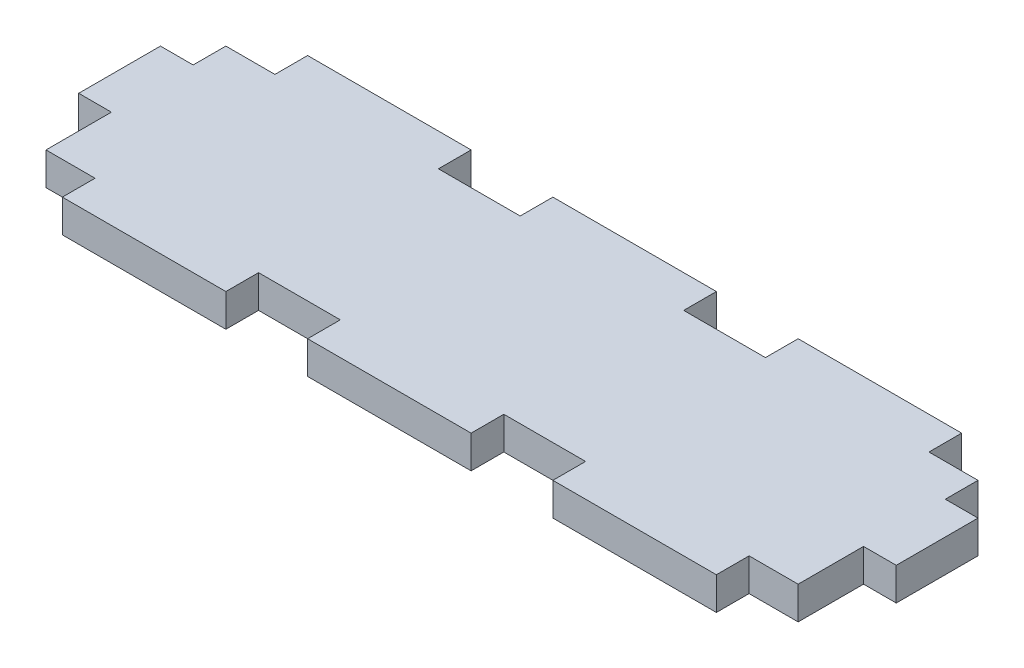
SolidWorks part; units mm, degrees
ref_plane "Front Plane" through (0, 0, 0) normal (0, 0, 1) x (1, 0, 0)
ref_plane "Top Plane" through (0, 0, 0) normal (0, 1, 0) x (1, 0, 0)
ref_plane "Right Plane" through (0, 0, 0) normal (1, 0, 0) x (0, 0, -1)
sketch "Sketch1" plane through (0, 0, 0) normal (0, 1, 0) x (1, 0, 0)
  line L1 (63.5, -19.05) -> (-63.5, -19.05)
  line L2 (63.5, -19.05) -> (63.5, 19.05)
  line L3 (63.5, 19.05) -> (-63.5, 19.05)
  line L4 (-63.5, -19.05) -> (-63.5, 19.05)
  line L5 (63.5, -19.05) -> (-63.5, 19.05) construction
  line L6 (63.5, 19.05) -> (-63.5, -19.05) construction
  point P0 (0, 0)
  dimension "D1" = 127
  dimension "D2" = 38.1
extrude "Boss-Extrude1" add sketch "Sketch1" along normal mid plane 5.08
sketch "Sketch2" plane through (0, 2.54, 0) normal (0, 1, 0) x (1, 0, 0)
  line L0 (63.5, 19.05) -> (-63.5, 19.05) construction
  line L1 (-63.5, 19.05) -> (-58.42, 19.05)
  line L2 (-63.5, 19.05) -> (-63.5, 8.89)
  line L3 (-63.5, 8.89) -> (-58.42, 8.89)
  line L4 (-58.42, 19.05) -> (-58.42, 8.89)
  line L5 (-63.5, 19.05) -> (-58.42, 8.89) construction
  line L6 (-63.5, 8.89) -> (-58.42, 19.05) construction
  line L7 (-63.5, 19.05) -> (-63.5, -19.05) construction
  line L8 (-63.5, -19.05) -> (63.5, -19.05) construction
  line L9 (-63.5, -3.81) -> (-58.42, -3.81)
  line L10 (-63.5, -3.81) -> (-63.5, -19.05)
  line L11 (-63.5, -19.05) -> (-58.42, -19.05)
  line L12 (-58.42, -3.81) -> (-58.42, -19.05)
  line L13 (-63.5, -3.81) -> (-58.42, -19.05) construction
  line L14 (-63.5, -19.05) -> (-58.42, -3.81) construction
  point P0 (-60.96, 13.97)
  point P9 (-60.96, -11.43)
  dimension "D1" = 5.08
  dimension "D2" = 10.16
  dimension "D3" = 12.7
  dimension "D4" = 5.08
extrude "Cut-Extrude1" cut sketch "Sketch2" against normal blind 5.08
mirror "Mirror1" about plane through (0, 0, 0) normal (1, 0, 0) of "Cut-Extrude1"
sketch "Sketch3" plane through (0, 2.54, 0) normal (0, 1, 0) x (1, 0, 0)
  line L0 (-58.42, -19.05) -> (58.42, -19.05) construction
  line L1 (-63.5, -13.97) -> (-50.8, -13.97)
  line L2 (-63.5, -13.97) -> (-63.5, -19.05)
  line L3 (-63.5, -19.05) -> (-50.8, -19.05)
  line L4 (-50.8, -13.97) -> (-50.8, -19.05)
  line L5 (-63.5, -13.97) -> (-50.8, -19.05) construction
  line L6 (-63.5, -19.05) -> (-50.8, -13.97) construction
  line L7 (-63.5, 8.89) -> (-63.5, -3.81) construction
  point P0 (-57.15, -16.51)
  dimension "D1" = 5.08
  dimension "D2" = 0
  dimension "D3" = 12.7
extrude "Cut-Extrude2" cut sketch "Sketch3" against normal up to surface (5.08 mm away) up to face at (0, -2.54, -1.6933)
mirror "Mirror2" about plane through (0, 0, 0) normal (1, 0, 0) of "Cut-Extrude2"
sketch "Sketch4" plane through (0, 2.54, 0) normal (0, 1, 0) x (1, 0, 0)
  line L0 (-50.8, -19.05) -> (50.8, -19.05) construction
  line L1 (-25.4, -13.97) -> (-12.7, -13.97)
  line L2 (-25.4, -13.97) -> (-25.4, -19.05)
  line L3 (-25.4, -19.05) -> (-12.7, -19.05)
  line L4 (-12.7, -13.97) -> (-12.7, -19.05)
  line L5 (-25.4, -13.97) -> (-12.7, -19.05) construction
  line L6 (-25.4, -19.05) -> (-12.7, -13.97) construction
  line L7 (-50.8, -19.05) -> (-50.8, -13.97) construction
  point P0 (-19.05, -16.51)
  dimension "D1" = 25.4
  dimension "D2" = 12.7
  dimension "D3" = 5.08
extrude "Cut-Extrude4" cut sketch "Sketch4" against normal up to surface (5.08 mm away) up to face at (0, -2.54, 2.2225)
pattern_linear "LPattern1" count 2 spacing 38.1 along (1, 0, 0) of "Cut-Extrude4"
sketch "Sketch7" plane through (0, 2.54, 0) normal (0, 1, 0) x (1, 0, 0)
  line L0 (58.42, 19.05) -> (-58.42, 19.05) construction
  line L1 (-58.42, 19.05) -> (58.42, 19.05)
  line L2 (-58.42, 19.05) -> (-58.42, 13.97)
  line L3 (-58.42, 13.97) -> (58.42, 13.97)
  line L4 (58.42, 19.05) -> (58.42, 13.97)
  line L5 (-58.42, 8.89) -> (-58.42, 19.05) construction
  line L6 (58.42, 8.89) -> (58.42, 19.05) construction
  dimension "D1" = 5.08
extrude "Cut-Extrude7" cut sketch "Sketch7" against normal up to surface (5.08 mm away) up to face at (0, -2.54, 6.985)
sketch "Sketch8" plane through (0, 2.54, 0) normal (0, 1, 0) x (1, 0, 0)
  line L0 (-58.42, 13.97) -> (58.42, 13.97) construction
  line L1 (-50.8, 19.05) -> (-25.4, 19.05)
  line L2 (-50.8, 19.05) -> (-50.8, 13.97)
  line L3 (-50.8, 13.97) -> (-25.4, 13.97)
  line L4 (-25.4, 19.05) -> (-25.4, 13.97)
  line L6 (-50.8, -19.05) -> (-50.8, -13.97) construction
  line L8 (-25.4, -13.97) -> (-25.4, -19.05) construction
  line L9 (-12.7, -19.05) -> (-12.7, -13.97) construction
  line L10 (-12.7, 13.97) -> (12.7, 13.97)
  line L11 (-12.7, 13.97) -> (-12.7, 19.05)
  line L12 (-12.7, 19.05) -> (12.7, 19.05)
  line L13 (12.7, 13.97) -> (12.7, 19.05)
  line L14 (12.7, -13.97) -> (12.7, -19.05) construction
  line L15 (25.4, -19.05) -> (25.4, -13.97) construction
  line L16 (25.4, 13.97) -> (50.8, 13.97)
  line L17 (25.4, 13.97) -> (25.4, 19.05)
  line L18 (25.4, 19.05) -> (50.8, 19.05)
  line L19 (50.8, 13.97) -> (50.8, 19.05)
  line L20 (50.8, -19.05) -> (50.8, -13.97) construction
  dimension "D1" = 5.08
  dimension "D2" = 0
  dimension "D3" = 0
  dimension "D4" = 0
  dimension "D5" = 0
  dimension "D6" = 5.08
  dimension "D7" = 0
  dimension "D8" = 0
  dimension "D9" = 5.08
extrude "Boss-Extrude2" add sketch "Sketch8" against normal up to surface (5.08 mm away) up to face at (0, -2.54, 7.4083)
